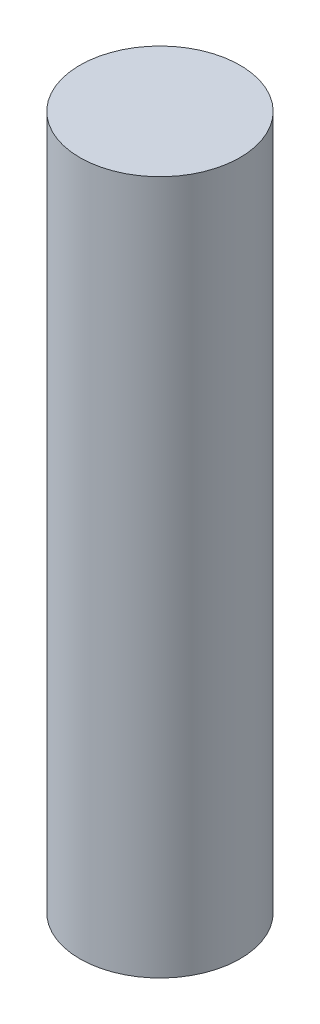
SolidWorks part; units mm, degrees
ref_plane "Front Plane" through (0, 0, 0) normal (0, 0, 1) x (1, 0, 0)
ref_plane "Top Plane" through (0, 0, 0) normal (0, 1, 0) x (1, 0, 0)
ref_plane "Right Plane" through (0, 0, 0) normal (1, 0, 0) x (0, 0, -1)
sketch "Sketch1" plane through (0, 0, 0) normal (0, 1, 0) x (1, 0, 0)
  circle A0 centre (0, 0) radius 3
extrude "Boss-Extrude1" add sketch "Sketch1" along normal blind 26
